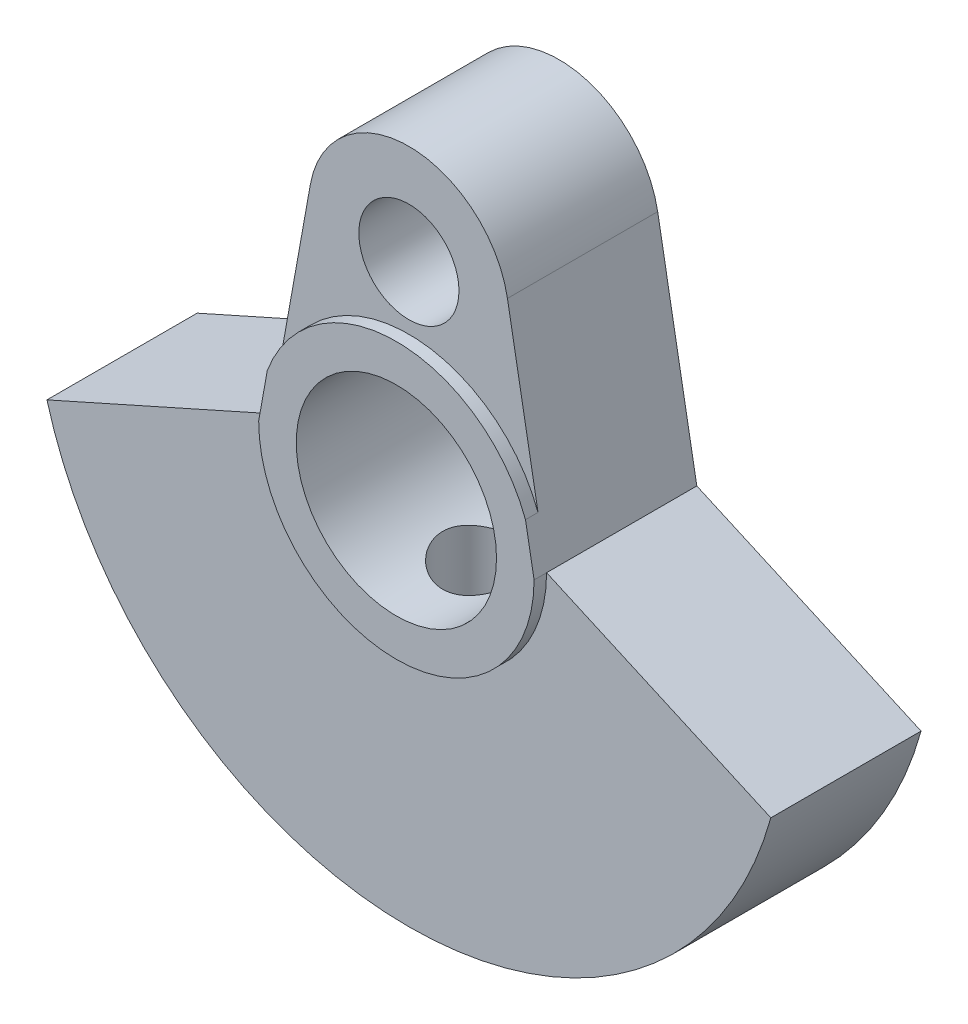
SolidWorks part; units mm, degrees
ref_plane "Front Plane" through (0, 0, 0) normal (0, 0, 1) x (1, 0, 0)
ref_plane "Top Plane" through (0, 0, 0) normal (0, 1, 0) x (1, 0, 0)
ref_plane "Right Plane" through (0, 0, 0) normal (1, 0, 0) x (0, 0, -1)
sketch "Эскиз1" plane through (0, 0, 0) normal (0, 0, 1) x (1, 0, 0)
  line L0 (-5.5, 0) -> (-3.9371, 8.7067)
  line L1 (0, 8) -> (0, 0) construction
  line L2 (5.5, 0) -> (3.9371, 8.7067)
  line L3 (-15, 0) -> (5.5, 0) construction
  line L4 (-5.5, 0) -> (-14.4568, -4)
  line L5 (5.5, 0) -> (14.4568, -4)
  arc A0 (-14.4568, -4) -> (14.4568, -4) centre (0, 0) ccw
  circle A1 centre (0, 0) radius 4
  circle A3 centre (0, 8) radius 2
  arc A5 (3.9371, 8.7067) -> (-3.9371, 8.7067) centre (0, 8) ccw
  point P8 (-5.5, 0)
  point P9 (5.5, 0)
  dimension "D1" = 30
  dimension "D2" = 8
  dimension "D4" = 4
  dimension "D5" = 4
  dimension "D6" = 8
  dimension "D7" = 4
extrude "Бобышка-Вытянуть1" add sketch "Эскиз1" along normal blind 6
sketch "Эскиз2" plane through (0, 0, 6) normal (0, 0, 1) x (1, 0, 0)
  line L0 (5.1566, 1.9129) -> (5.5, 0)
  line L2 (-5.1566, 1.9129) -> (-5.5, 0)
  arc A0 (5.1566, 1.9129) -> (-5.1566, 1.9129) centre (0, 0) ccw
  arc A1 (-5.5, 0) -> (5.5, 0) centre (0, 0) ccw
  circle A2 centre (0, 0) radius 4
extrude "Бобышка-Вытянуть2" add sketch "Эскиз2" along normal blind 0.5
ref_plane "Плоскость1" through (0, -15, 0) normal (0, 1, 0) x (1, 0, 0)
sketch "Эскиз3" plane through (0, -15, 0) normal (0, 1, 0) x (1, 0, 0)
  line L0 (0, 0) -> (0, -4.6406) construction
  line L2 (-14.4568, -6) -> (14.4568, -6) construction
  point P0 (0, -3)
  dimension "D1" = 3
ref_plane "Плоскость2" through (0, -10, 0) normal (0, 1, 0) x (1, 0, 0)
sketch "Эскиз5" plane through (0, -10, 0) normal (0, 1, 0) x (1, 0, 0)
  circle A0 centre (0, -3) radius 2.7471
extrude "Бобышка-Вытянуть3" add sketch "Эскиз5" against normal blind 6.5
hole_wizard "Отверстие обработанное метчиком M41" positions "Эскиз6" profile "Эскиз7" tap size "M4" standard "DIN"
sketch "Эскиз6" plane through (0, -16.5, 0) normal (0, -1, 0) x (-1, 0, 0)
  point P0 (0, -3)
sketch "Эскиз7" plane through (0, -16.5, 3) normal (1, 0, 0) x (0, 0, -1)
  line L0 (0, 0) -> (0, 17.4904)
  line L1 (0, 17.4904) -> (1.65, 16.499)
  line L2 (1.65, 16.499) -> (1.65, 0)
  line L5 (1.65, 0) -> (0, 0)
  line L10 (0, 17.4904) -> (-1.65, 16.499) construction
  line L11 (0, -6.35) -> (0, 107.95) construction
  dimension "Диаметр сверла" = 3.3
  dimension "Глубина сверла" = 16.499
  dimension "Угол заточки сверла" = 118
cosmetic thread "Отверстие резьбы2" parameters "D1"=16, "D2"=4
sketch "Эскиз8" plane through (0, 0, 6) normal (0, 0, 1) x (1, 0, 0)
  line L0 (-5.4636, -13.9696) -> (-5.4636, -17.4215)
  line L1 (5.4636, -13.9696) -> (5.4636, -17.4215)
  arc A0 (-5.4636, -13.9696) -> (5.4636, -13.9696) centre (0, 0) ccw
  arc A1 (-5.4636, -17.4215) -> (5.4636, -17.4215) centre (0, 0) ccw
extrude "Вырез-Вытянуть1" cut sketch "Эскиз8" against normal blind 6.5
